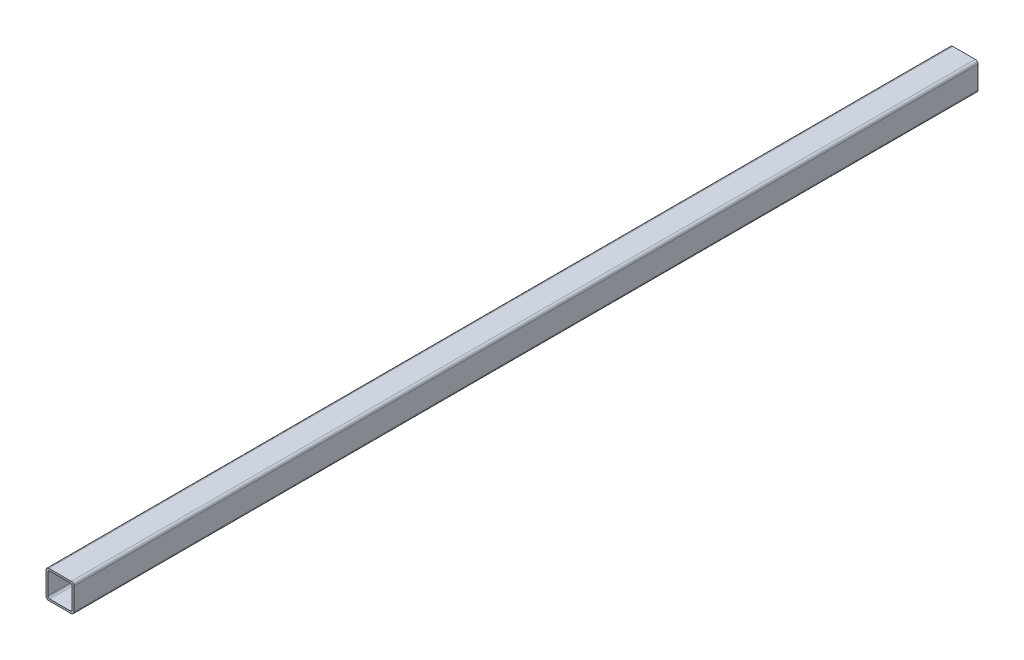
SolidWorks part; units mm, degrees
material "AISI 1020"
ref_plane "Спереди" through (0, 0, 0) normal (0, 0, 1) x (1, 0, 0)
ref_plane "Сверху" through (0, 0, 0) normal (0, 1, 0) x (1, 0, 0)
ref_plane "Справа" through (0, 0, 0) normal (1, 0, 0) x (0, 0, -1)
sketch "Эскиз1" plane through (0, 0, 0) normal (0, 0, 1) x (1, 0, 0)
  line L0 (-12, 15) -> (12, 15) construction
  line L1 (15, 12) -> (15, -12) construction
  line B0 (-12, 15) -> (12, 15)
  line B1 (-15, 12) -> (-15, -12)
  line B2 (-12, -15) -> (12, -15)
  line B3 (15, 12) -> (15, -12)
  line B4 (-11, 13) -> (11, 13)
  line B5 (-13, 11) -> (-13, -11)
  line B6 (-11, -13) -> (11, -13)
  line B7 (13, 11) -> (13, -11)
  arc B8 (-15, -12) -> (-12, -15) centre (-12, -12) ccw
  arc B9 (12, -15) -> (15, -12) centre (12, -12) ccw
  arc B10 (12, 15) -> (15, 12) centre (12, 12) cw
  arc B11 (-12, 15) -> (-15, 12) centre (-12, 12) ccw
  arc B12 (-13, -11) -> (-11, -13) centre (-11, -11) ccw
  arc B13 (11, -13) -> (13, -11) centre (11, -11) ccw
  arc B14 (11, 13) -> (13, 11) centre (11, 11) cw
  arc B15 (-11, 13) -> (-13, 11) centre (-11, 11) ccw
sketch_block_instance "Блок-30х30х2-1"
sketch_block "Блок-30х30х2" parameters "D3"=3, "D4"=2, "D1"=30, "D2"=2
extrude "Бобышка-Вытянуть1" add sketch "Эскиз1" along normal offset from surface (484.6 mm away) 7
mirror "Зеркальное отражение1" about plane through (-12, -12, 0) normal (0, 0, 1) of bodies 103
